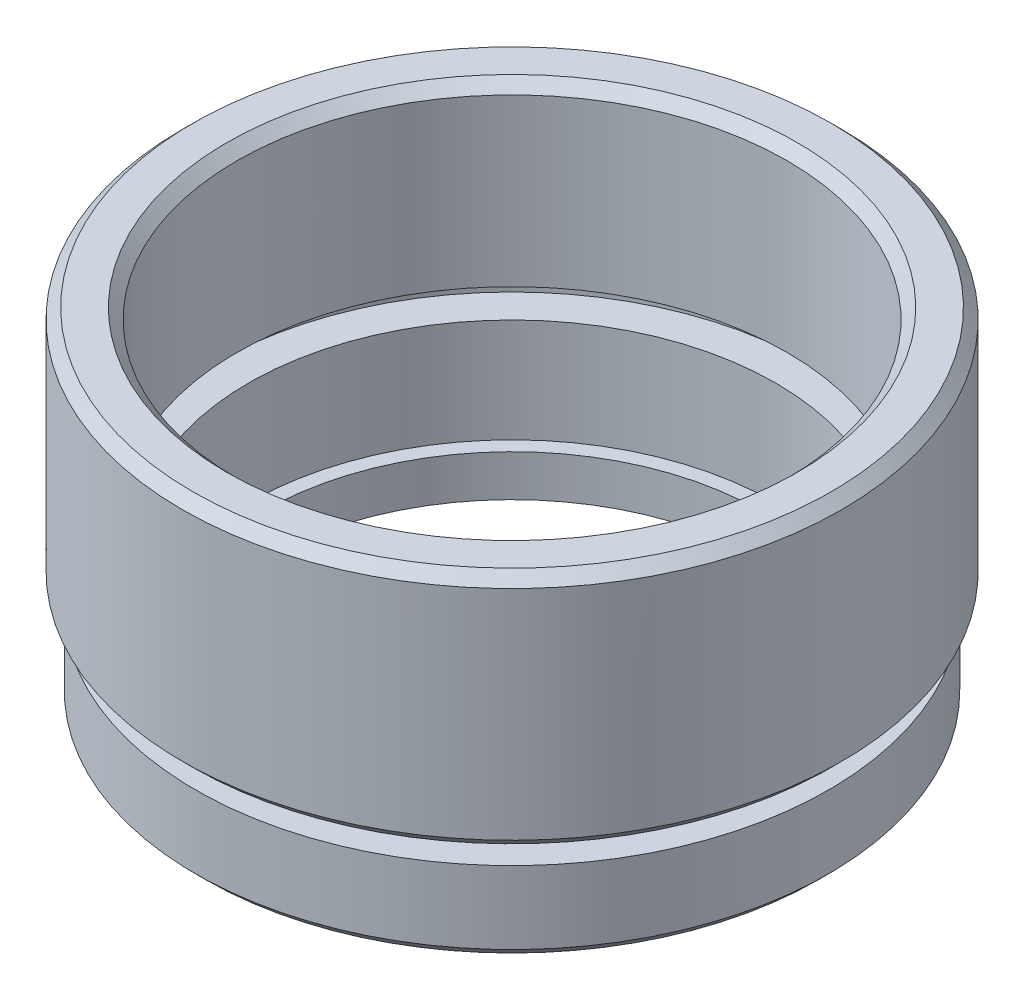
SolidWorks part; units mm, degrees
ref_plane "前视基准面" through (0, 0, 0) normal (0, 0, 1) x (1, 0, 0)
ref_plane "上视基准面" through (0, 0, 0) normal (0, 1, 0) x (1, 0, 0)
ref_plane "右视基准面" through (0, 0, 0) normal (1, 0, 0) x (0, 0, -1)
sketch "草图1" plane through (0, 0, 0) normal (0, 0, 1) x (1, 0, 0)
  line L0 (0, 0) -> (0, 21.8535) construction
  line L1 (12, 0) -> (15.25, 0)
  line L2 (15.25, 0) -> (15.25, 4)
  line L3 (15.25, 4) -> (13.75, 4)
  line L4 (13.75, 4) -> (13.75, 5)
  line L5 (13.75, 5) -> (15.875, 5)
  line L6 (15.875, 5) -> (15.875, 16.5)
  line L7 (15.875, 16.5) -> (13.25, 16.5)
  line L8 (13.25, 16.5) -> (13.25, 8)
  line L9 (13.25, 8) -> (14.35, 8)
  line L10 (14.35, 8) -> (14.35, 7)
  line L11 (14.35, 7) -> (12.7, 7)
  line L12 (12.7, 7) -> (12.7, 2)
  line L13 (12.7, 2) -> (12, 2)
  line L14 (12, 0) -> (12, 2)
  dimension "D1" = 16.5
  dimension "D2" = 15.875
  dimension "D3" = 13.25
  dimension "D4" = 12.7
  dimension "D5" = 1
  dimension "D6" = 5
  dimension "D7" = 12
  dimension "D8" = 15.25
  dimension "D9" = 1
  dimension "D10" = 5
  dimension "D11" = 2
  dimension "D12" = 14.35
  dimension "D13" = 13.75
revolve "旋转1" add sketch "草图1" angle 360 about L0
cosmetic thread "装饰螺纹线11"
cosmetic thread "装饰螺纹线12"
chamfer "倒角1" distance 0.5 angle 45 4 edges at (0, 16.5, -13.25) (0, 16.5, -15.875) (0, 5, -15.875) (0, 0, -15.25)
